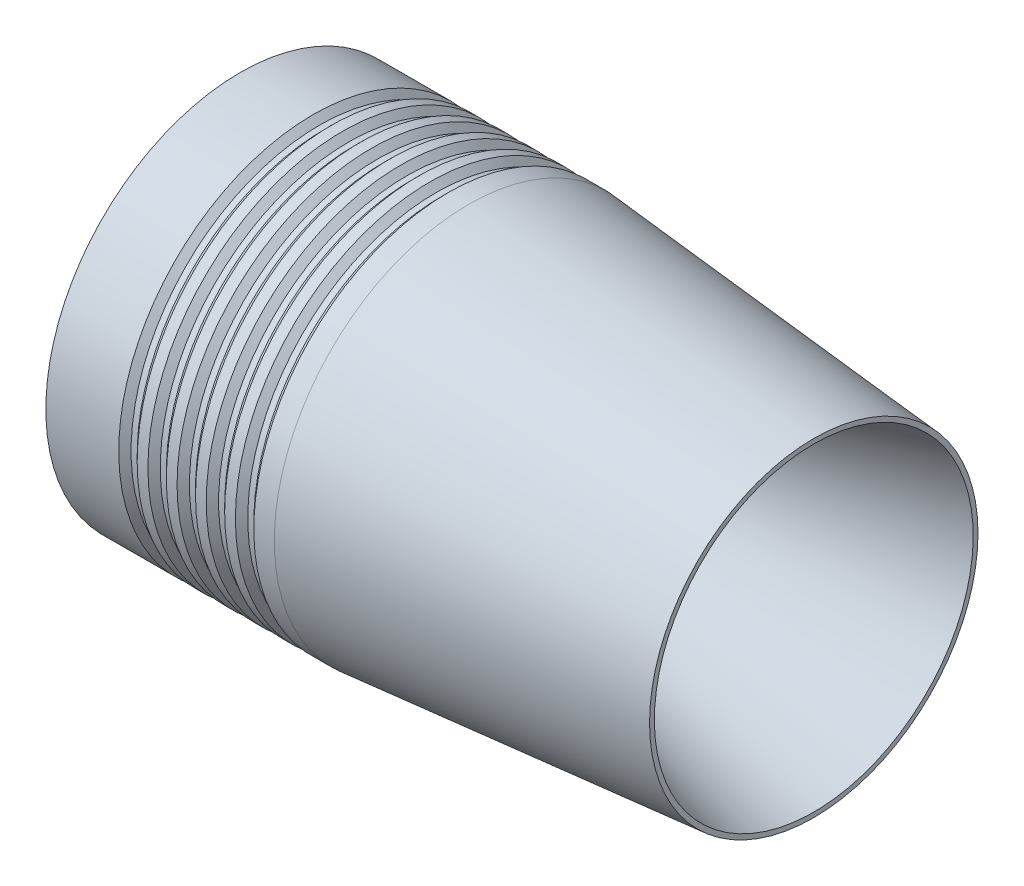
SolidWorks part; units mm, degrees
material "Custom Plastic"
ref_plane "Front Plane" through (0, 0, 0) normal (0, 0, 1) x (1, 0, 0)
ref_plane "Top Plane" through (0, 0, 0) normal (0, 1, 0) x (1, 0, 0)
ref_plane "Right Plane" through (0, 0, 0) normal (1, 0, 0) x (0, 0, -1)
sketch "Sketch1" plane through (0, 0, 0) normal (0, 0, 1) x (1, 0, 0)
  line L0 (0, 0) -> (0, 17.653) construction
  line L1 (0, 17.653) -> (0, 24.511) construction
  line L2 (0, 17.653) -> (0, 44.323) construction
  line L3 (0, 0) -> (90.17, 0) construction
  line L4 (90.17, 0) -> (90.17, 41.656) construction
  line L5 (1.7808, 17.8883) -> (90.17, 41.656)
  line L6 (0, 0) -> (-59.69, 0) construction
  line L7 (-59.69, 0) -> (-59.69, 38.1) construction
  line L8 (-59.69, 38.1) -> (-9.3108, 19.3311)
  line L9 (-59.69, 38.1) -> (90.17, 41.656)
  line L10 (-59.69, 38.1) -> (-59.69, 50.8)
  line L11 (90.17, 41.656) -> (90.17, 50.8)
  line L12 (-59.69, 50.8) -> (90.17, 50.8)
  line L13 (0, 0) -> (0, 50.8) construction
  line L14 (0, 50.8) -> (90.17, 42.9111)
  line L16 (-59.69, 38.1) -> (-72.39, 38.1)
  line L17 (-59.69, 38.1) -> (-59.69, 44.45)
  line L18 (-59.69, 44.45) -> (-72.39, 44.45)
  line L19 (-72.39, 38.1) -> (-72.39, 44.45)
  arc A0 (-9.3108, 19.3311) -> (0, 17.653) centre (0, 44.323) ccw
  arc A1 (0, 17.653) -> (1.7808, 17.8883) centre (0, 24.511) ccw
  dimension "D1" = 17.653
  dimension "D2" = 6.858
  dimension "D3" = 26.67
  dimension "D4" = 90.17
  dimension "D5" = 41.656
  dimension "D6" = 59.69
  dimension "D7" = 38.1
  dimension "D8" = 12.7
  dimension "D9" = 5
  dimension "D10" = 12.7
  dimension "D11" = 6.35
revolve "Revolve1" add sketch "Sketch1" angle 360 about L6
sketch "Sketch2" plane through (0, 0, 0) normal (0, 0, 1) x (1, 0, 0)
  line L0 (0, 0) -> (0, 54.9657) construction
  line L1 (0, 31.75) -> (-50.8, 31.75)
  line L2 (0, 31.75) -> (25.4, 31.75)
  line L3 (25.4, 31.75) -> (25.4, 0)
  line L4 (25.4, 0) -> (0, 0)
  line L5 (-50.8, 31.75) -> (-50.8, 0)
  line L6 (-50.8, 0) -> (0, 0)
  line L7 (-59.69, 38.1) -> (-9.3108, 19.3311) construction
  line L8 (-59.69, 38.1) -> (-9.3108, 19.3311) construction
  line L9 (-42.6455, 31.75) -> (-42.6455, 35.56)
  line L10 (-42.6455, 35.56) -> (-29.0855, 35.56)
  line L11 (-29.0855, 35.56) -> (25.4, 31.75)
  dimension "D1" = 31.75
  dimension "D2" = 25.4
  dimension "D3" = 50.8
  dimension "D4" = 35.56
  dimension "D5" = 4
revolve "Cut-Revolve2" cut sketch "Sketch2" angle 360 about L6
sketch "Sketch4" plane through (0, 0, 0) normal (0, 0, 1) x (1, 0, 0)
  line L0 (0, 0) -> (-42.6455, 0) construction
  line L2 (-42.6455, 0) -> (-42.6455, 31.75) construction
  line L3 (-72.39, 44.45) -> (-72.39, -44.45) construction
  line L4 (-42.6455, 31.75) -> (-72.39, 31.75)
  line L5 (-42.6455, 31.75) -> (-42.6455, 44.45)
  line L6 (-42.6455, 44.45) -> (-72.39, 44.45)
  line L7 (-72.39, 31.75) -> (-72.39, 44.45)
  dimension "D1" = 31.75
  dimension "D2" = 12.7
  dimension "D3" = 42.6455
revolve "Cut-Revolve4" cut sketch "Sketch4" angle 360 about L0
sketch "Sketch5" plane through (0, 0, 0) normal (0, 0, 1) x (1, 0, 0)
  line L0 (0, 0) -> (-94.5242, 0) construction
  line L1 (0, 0) -> (0, 50.8) construction
  line L2 (0, 50.8) -> (0, -50.8) construction
  line L3 (0, 50.8) -> (-59.69, 50.8) construction
  line L4 (-37.4396, 49.1871) -> (-35.8267, 50.8)
  line L5 (-37.4396, 50.8) -> (-39.0271, 50.8)
  line L6 (-37.4396, 50.8) -> (-37.4396, 49.1871)
  line L7 (-37.4396, 49.1871) -> (-39.0271, 49.1871)
  line L8 (-39.0271, 50.8) -> (-39.0271, 49.1871)
  line L21 (-39.0271, 49.1871) -> (-40.64, 50.8)
  line L22 (-35.8267, 50.8) -> (-40.64, 50.8)
  line L23 (-59.69, 50.8) -> (-59.69, -50.8) construction
  dimension "D1" = 50.8
  dimension "D2" = 1.5875
  dimension "D3" = 45
  dimension "D4" = 1.6129
  dimension "D5" = 19.05
revolve "Cut-Revolve5" cut sketch "Sketch5" angle 360 about L0
pattern_linear "LPattern1" count 5 spacing 7.62 along (1, 0, 0) of "Cut-Revolve5"
